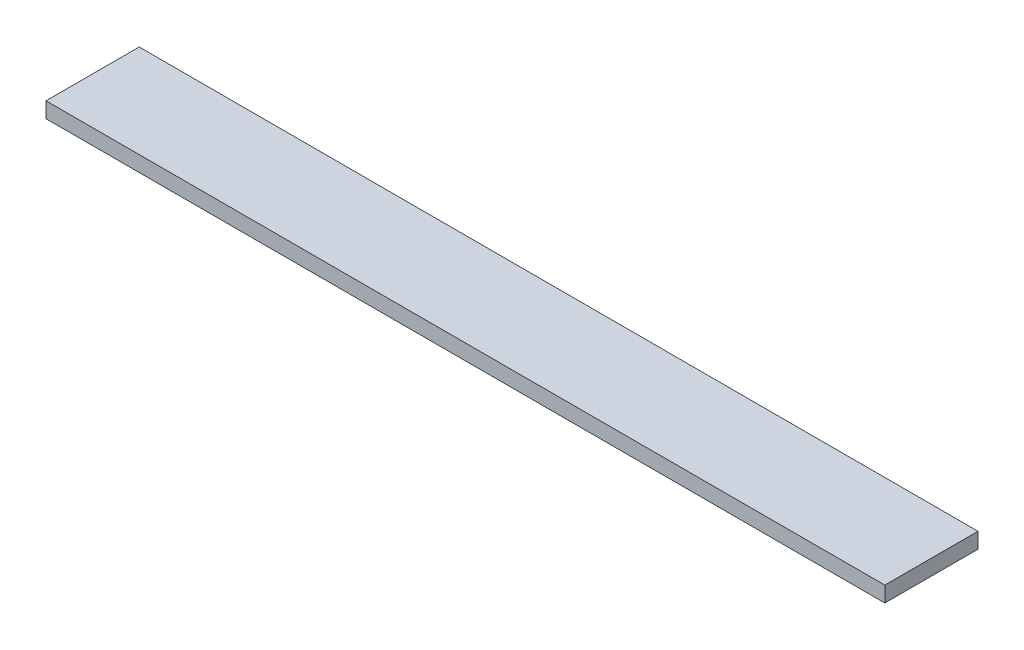
SolidWorks part; units mm, degrees
ref_plane "Front Plane" through (0, 0, 0) normal (0, 0, 1) x (1, 0, 0)
ref_plane "Top Plane" through (0, 0, 0) normal (0, 1, 0) x (1, 0, 0)
ref_plane "Right Plane" through (0, 0, 0) normal (1, 0, 0) x (0, 0, -1)
sketch "Sketch1" plane through (0, 0, 0) normal (0, 1, 0) x (1, 0, 0)
  line L1 (-685.8, -76.2) -> (0, -76.2)
  line L2 (-685.8, -76.2) -> (-685.8, 0)
  line L3 (-685.8, 0) -> (0, 0)
  line L4 (0, -76.2) -> (0, 0)
  dimension "D1" = 685.8
  dimension "D2" = 76.2
extrude "Boss-Extrude1" add sketch "Sketch1" along normal blind 12.7
